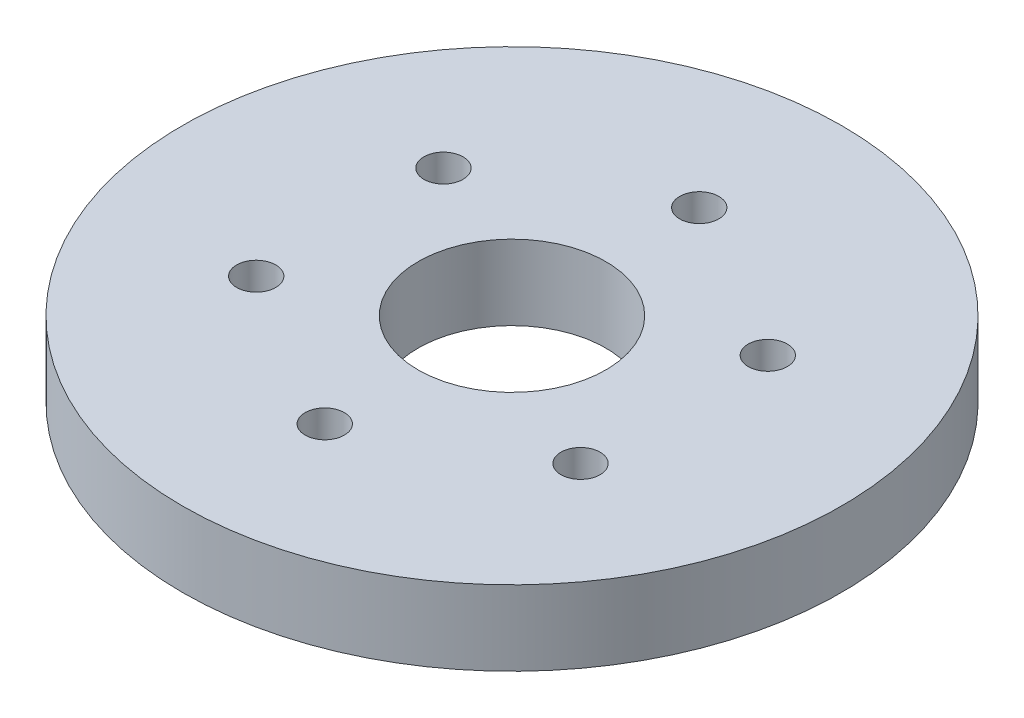
SolidWorks part; units mm, degrees
material "Plain Carbon Steel"
ref_plane "Front Plane" through (0, 0, 0) normal (0, 0, 1) x (1, 0, 0)
ref_plane "Top Plane" through (0, 0, 0) normal (0, 1, 0) x (1, 0, 0)
ref_plane "Right Plane" through (0, 0, 0) normal (1, 0, 0) x (0, 0, -1)
ref_plane "Plane1" through (0, 0, 0) normal (0, -1, 0) x (1, 0, 0)
sketch "Sketch1" plane through (0, 0, 0) normal (0, -1, 0) x (1, 0, 0)
  circle A0 centre (-20.6222, -11.9062) radius 2.4892
  circle A1 centre (-20.6222, 11.9062) radius 2.4892
  circle A2 centre (0, 23.8125) radius 2.4892
  circle A3 centre (20.6222, 11.9062) radius 2.4892
  circle A4 centre (20.6222, -11.9062) radius 2.4892
  circle A5 centre (0, 0) radius 11.938
  circle A6 centre (0, -23.8125) radius 2.4892
  circle A7 centre (0, 0) radius 41.91
  dimension "D1" = 4.9784
  dimension "D2" = 23.876
  dimension "D3" = 83.82
  dimension "D4" = 4.9784
  dimension "D5" = 4.9784
  dimension "D6" = 4.9784
  dimension "D7" = 4.9784
  dimension "D8" = 4.9784
  dimension "D9" = 20.6222
  dimension "D10" = 41.2445
  dimension "D11" = 11.9062
  dimension "D12" = 23.8125
  dimension "D13" = 35.7188
  dimension "D14" = 47.625
extrude "Boss-Extrude1" add sketch "Sketch1" against normal blind 9.525
